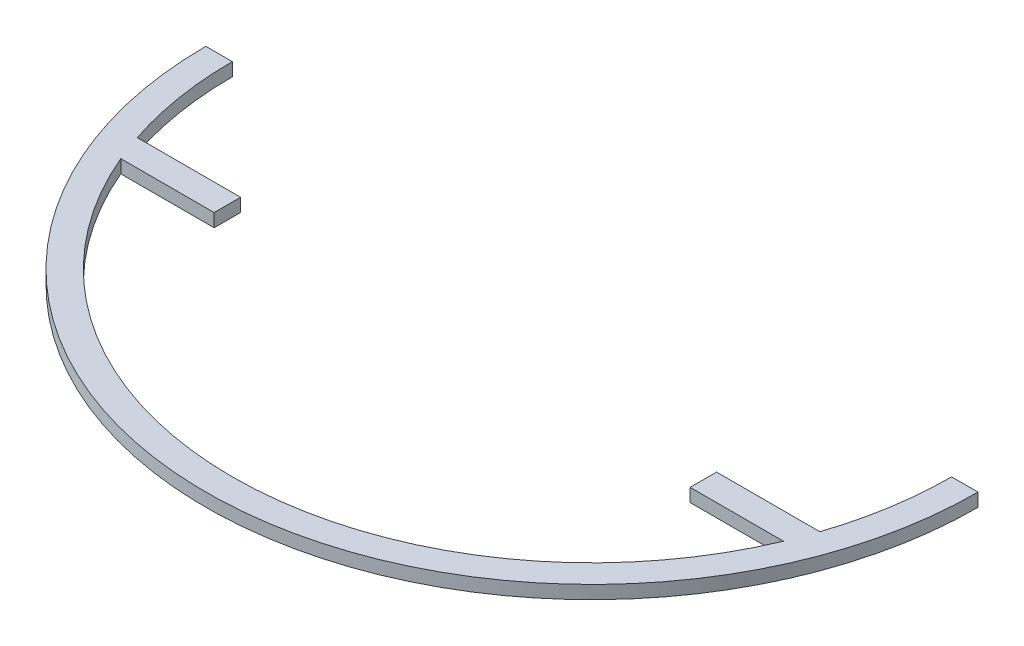
SolidWorks part; units mm, degrees
ref_plane "Front Plane" through (0, 0, 0) normal (0, 0, 1) x (1, 0, 0)
ref_plane "Top Plane" through (0, 0, 0) normal (0, 1, 0) x (1, 0, 0)
ref_plane "Right Plane" through (0, 0, 0) normal (1, 0, 0) x (0, 0, -1)
sketch "Sketch1" plane through (0, 0, 0) normal (0, 1, 0) x (1, 0, 0)
  line L0 (-92.71, 0) -> (-86.36, 0)
  line L5 (-81.9579, -27.2204) -> (-57.15, -27.2204)
  line L6 (-81.9579, -27.2204) -> (-81.9579, -33.5704)
  line L7 (-81.9579, -33.5704) -> (-57.15, -33.5704)
  line L8 (-57.15, -27.2204) -> (-57.15, -33.5704)
  line L9 (57.15, -27.2204) -> (81.9579, -27.2204)
  line L10 (57.15, -27.2204) -> (57.15, -33.5704)
  line L11 (57.15, -33.5704) -> (81.9579, -33.5704)
  line L12 (81.9579, -27.2204) -> (81.9579, -33.5704)
  line L13 (86.36, 0) -> (92.71, 0)
  line L14 (-57.15, 74.5841) -> (57.15, 74.5841) construction
  arc A0 (-92.71, 0) -> (92.71, 0) centre (0, 0) ccw
  arc A1 (-86.36, 0) -> (86.36, 0) centre (0, 0) ccw
  dimension "D2" = 6.35
  dimension "D3" = 6.35
  dimension "D4" = 6.35
  dimension "D5" = 185.42
  dimension "D6" = 114.3
extrude "Boss-Extrude1" add sketch "Sketch1" along normal blind 3.175 contours L5 A1 L7 L8 | A1 L12 L11 L7 L6 L0 A0 L13 | A1 L6 L7 | A1 L11 L12 | L11 A1 L9 L10
